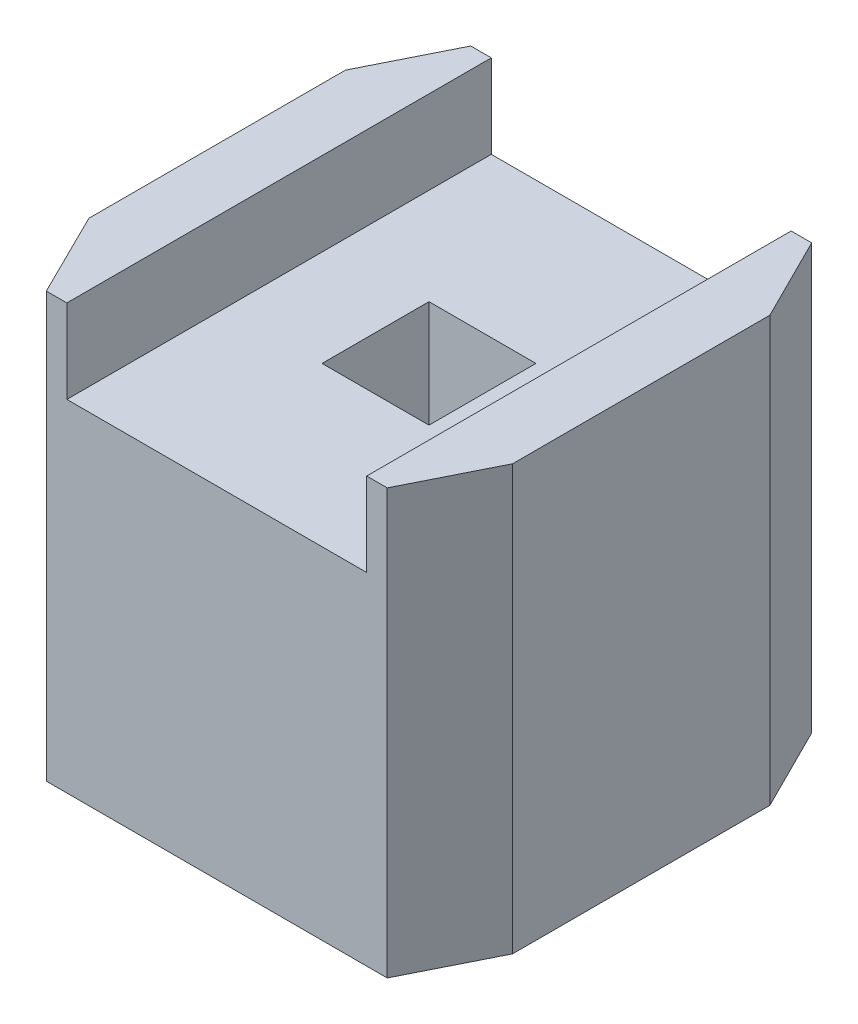
SolidWorks part; units mm, degrees
material "ABS"
ref_plane "Front Plane" through (0, 0, 0) normal (0, 0, 1) x (1, 0, 0)
ref_plane "Top Plane" through (0, 0, 0) normal (0, 1, 0) x (1, 0, 0)
ref_plane "Right Plane" through (0, 0, 0) normal (1, 0, 0) x (0, 0, -1)
sketch "Sketch1" plane through (0, 0, 0) normal (0, 1, 0) x (1, 0, 0)
  line L0 (-1.02, 1.27) -> (-1.27, 0.77)
  line L1 (-1.27, 0.77) -> (-1.27, -0.765)
  line L2 (-1.27, -0.765) -> (-1.02, -1.27)
  line L3 (-1.02, -1.27) -> (1.02, -1.27)
  line L4 (1.02, -1.27) -> (1.27, -0.77)
  line L5 (1.27, -0.77) -> (1.27, 0.77)
  line L6 (1.27, 0.77) -> (1.02, 1.27)
  line L7 (1.02, 1.27) -> (-1.02, 1.27)
  line L9 (0.32, -0.32) -> (-0.32, -0.32)
  line L10 (0.32, -0.32) -> (0.32, 0.32)
  line L11 (0.32, 0.32) -> (-0.32, 0.32)
  line L12 (-0.32, -0.32) -> (-0.32, 0.32)
  line L13 (0.32, -0.32) -> (-0.32, 0.32) construction
  line L14 (0.32, 0.32) -> (-0.32, -0.32) construction
  point P8 (0, 0)
extrude "Boss-Extrude1" add sketch "Sketch1" along normal blind 2.54
sketch "Sketch3" plane through (0, 2.54, 0) normal (0, 1, 0) x (1, 0, 0)
  line L0 (1.02, 1.27) -> (-1.02, 1.27) construction
  line L1 (0.8971, -1.27) -> (-0.8971, -1.27)
  line L2 (0.8971, -1.27) -> (0.8971, 1.27)
  line L3 (0.8971, 1.27) -> (-0.8971, 1.27)
  line L4 (-0.8971, -1.27) -> (-0.8971, 1.27)
  line L5 (0.8971, -1.27) -> (-0.8971, 1.27) construction
  line L6 (0.8971, 1.27) -> (-0.8971, -1.27) construction
  point P0 (0, 0)
extrude "Cut-Extrude1" cut sketch "Sketch3" against normal blind 0.5
